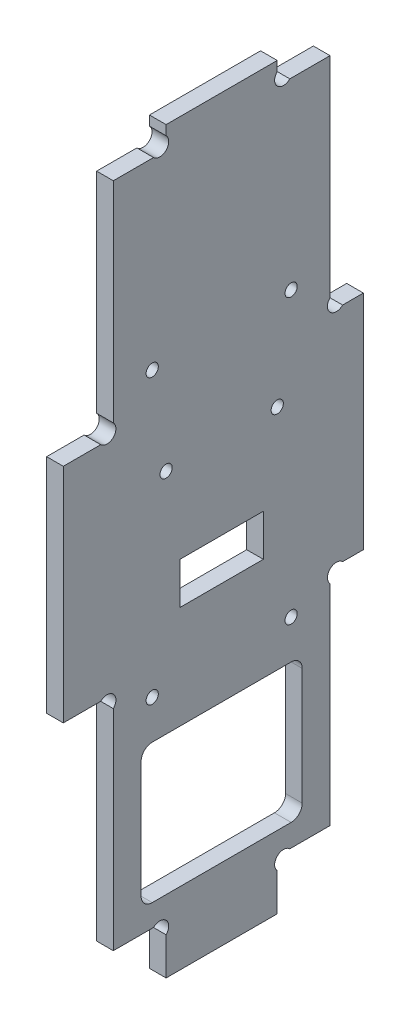
SolidWorks part; units mm, degrees
ref_plane "Plan de face" through (0, 0, 0) normal (0, 0, 1) x (1, 0, 0)
ref_plane "Plan de dessus" through (0, 0, 0) normal (0, 1, 0) x (1, 0, 0)
ref_plane "Plan de droite" through (0, 0, 0) normal (1, 0, 0) x (0, 0, -1)
sketch "Esquisse1" plane through (0, 0, 0) normal (1, 0, 0) x (0, 0, -1)
  line L13 (18.5, 6.7373) -> (18.5, 0)
  line L15 (16.2373, 9) -> (9, 9)
  line L17 (50.2627, 49) -> (54, 49)
  line L18 (6.7373, 49) -> (0, 49)
  line L19 (38.5, 6.7373) -> (38.5, 0)
  line L20 (50.2627, 89) -> (54, 89)
  line L21 (6.7373, 89) -> (0, 89)
  line L22 (18.5, 0) -> (38.5, 0)
  line L23 (40.7627, 9) -> (48, 9)
  line L24 (48, 9) -> (48, 46.7373)
  line L25 (9, 9) -> (9, 46.7373)
  line L26 (54, 89) -> (54, 49)
  line L27 (0, 49) -> (0, 89)
  line L29 (18.5, 131.2627) -> (18.5, 133)
  line L30 (38.5, 131.2627) -> (38.5, 133)
  line L31 (9, 91.2627) -> (9, 129)
  line L32 (9, 129) -> (16.2373, 129)
  line L33 (18.5, 133) -> (38.5, 133)
  line L34 (40.7627, 129) -> (48, 129)
  line L35 (48, 129) -> (48, 91.2627)
  arc A0 (50.2627, 49) -> (48, 46.7373) centre (49.1314, 47.8686) ccw
  arc A1 (9, 46.7373) -> (6.7373, 49) centre (7.8686, 47.8686) ccw
  arc A2 (18.5, 6.7373) -> (16.2373, 9) centre (17.3686, 7.8686) ccw
  arc A3 (38.5, 6.7373) -> (40.7627, 9) centre (39.6314, 7.8686) cw
  arc A4 (9, 91.2627) -> (6.7373, 89) centre (7.8686, 90.1314) cw
  arc A5 (50.2627, 89) -> (48, 91.2627) centre (49.1314, 90.1314) cw
  arc A6 (16.2373, 129) -> (18.5, 131.2627) centre (17.3686, 130.1314) ccw
  arc A7 (40.7627, 129) -> (38.5, 131.2627) centre (39.6314, 130.1314) cw
  point P1 (12.6186, 9)
  dimension "D14" = 1.1314
  dimension "D15" = 1.1314
  dimension "D17" = 1.1314
  dimension "D23" = 1.1314
  dimension "D10" = 1.6
  dimension "D1" = 6
  dimension "D2" = 9
  dimension "D3" = 9.5
  dimension "D4" = 9.5
  dimension "D5" = 9
  dimension "D6" = 40
  dimension "D7" = 40
  dimension "D8" = 40
  dimension "D9" = 4
  dimension "D11" = 1.1314
  dimension "D12" = 1.1314
  dimension "D13" = 1.1314
  dimension "D16" = 20
  dimension "D18" = 1.1314
  dimension "D19" = 1.1314
  dimension "D20" = 1.1314
  dimension "D21" = 1.1314
  dimension "D22" = 1.1314
  dimension "D24" = 3.7373
  dimension "D25" = 1.7373
  dimension "D26" = 1.1314
  dimension "D27" = 7.2373
  dimension "D28" = 1.1314
  dimension "D29" = 1.7373
  dimension "D30" = 20
  dimension "D31" = 39
  dimension "D32" = 39
extrude "Extrusion1" add sketch "Esquisse1" along normal blind 3
sketch "Esquisse2" plane through (0, 0, 0) normal (-1, 0, 0) x (0, 0, 1)
  line L0 (-48, 9) -> (-48, 46.7373) construction
  line L1 (-9, 9) -> (-16.2373, 9) construction
  line L2 (-9, 46.7373) -> (-9, 9) construction
  line L3 (-40.7627, 9) -> (-48, 9) construction
  line L4 (-14, 38) -> (-43, 38)
  line L5 (-14, 38) -> (-14, 13)
  line L6 (-14, 13) -> (-43, 13)
  line L7 (-43, 38) -> (-43, 13)
  line L8 (-48, 9) -> (-48, 46.7373) construction
  line L9 (-9, 46.7373) -> (-9, 9) construction
  circle A0 centre (-38.5, 79) radius 1.1
  circle A1 centre (-18.5, 79) radius 1.1
  dimension "D1" = 2.2
  dimension "D2" = 9.5
  dimension "D3" = 20
  dimension "D4" = 9.5
  dimension "D5" = 70
  dimension "D6" = 4
  dimension "D7" = 5
  dimension "D8" = 5
  dimension "D9" = 25
extrude "Enlèv. mat.-Extru.1" cut sketch "Esquisse2" against normal through all
fillet "Congé1" radius 2 4 edges at (1.5, 13, -43) (1.5, 13, -14) (1.5, 38, -14) (1.5, 38, -43)
sketch "Esquisse3" plane through (0, 0, 0) normal (-1, 0, 0) x (0, 0, 1)
  line L1 (-36, 64) -> (-21, 64)
  line L2 (-36, 64) -> (-36, 56.5)
  line L3 (-36, 56.5) -> (-21, 56.5)
  line L4 (-21, 64) -> (-21, 56.5)
  circle A0 centre (-38.5, 79) radius 1.1 construction
  circle A1 centre (-18.5, 79) radius 1.1 construction
  dimension "D1" = 15
  dimension "D2" = 7.5
  dimension "D3" = 2.5
  dimension "D4" = 2.5
  dimension "D5" = 15
extrude "Enlèv. mat.-Extru.2" cut sketch "Esquisse3" against normal through all
sketch "Esquisse4" plane through (0, 0, 0) normal (-1, 0, 0) x (0, 0, 1)
  line L0 (-36, 64) -> (-36, 56.5) construction
  line L1 (-21, 56.5) -> (-21, 64) construction
  line L2 (-14, 15) -> (-14, 36) construction
  line L3 (-16, 38) -> (-41, 38) construction
  line L4 (-43, 36) -> (-43, 15) construction
  line L5 (-36, 64) -> (-36, 56.5) construction
  circle A0 centre (-41, 96) radius 1.1
  circle A1 centre (-16, 96) radius 1.1
  circle A2 centre (-18.5, 79) radius 1.1 construction
  circle A3 centre (-41, 45) radius 1.1
  circle A4 centre (-16, 45) radius 1.1
  dimension "D1" = 2.2
  dimension "D2" = 5
  dimension "D3" = 5
  dimension "D4" = 17
  dimension "D5" = 7
  dimension "D6" = 2
  dimension "D7" = 2
  dimension "D8" = 5
extrude "Enlèv. mat.-Extru.3" cut sketch "Esquisse4" against normal through all
